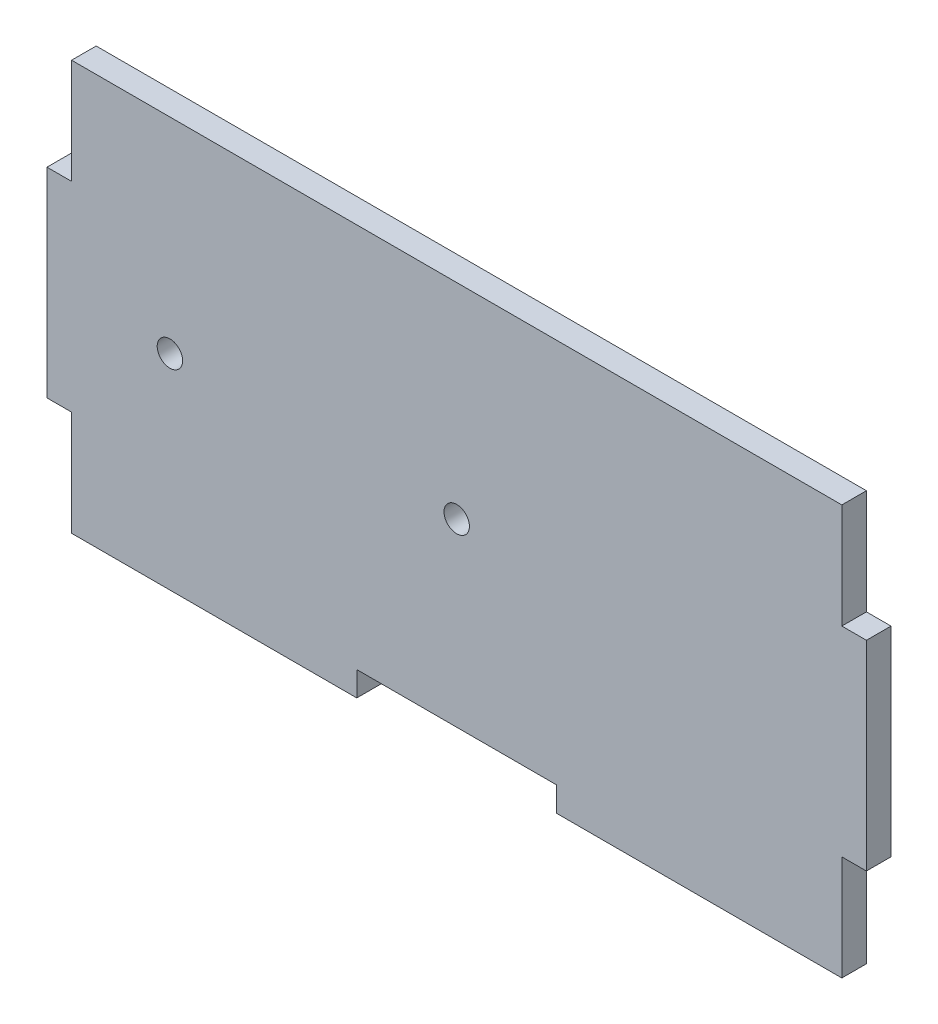
SolidWorks part; units mm, degrees
ref_plane "Alzado" through (0, 0, 0) normal (0, 0, 1) x (1, 0, 0)
ref_plane "Planta" through (0, 0, 0) normal (0, 1, 0) x (1, 0, 0)
ref_plane "Vista lateral" through (0, 0, 0) normal (1, 0, 0) x (0, 0, -1)
sketch "Model" plane through (0, 0, 0) normal (0, 0, 1) x (1, 0, 0)
  line L0 (186, 103) -> (186, 90.195)
  line L1 (186, 90.195) -> (183, 90.195)
  line L2 (183, 90.195) -> (183, 65.805)
  line L3 (183, 65.805) -> (186, 65.805)
  line L4 (186, 65.805) -> (186, 53)
  line L5 (186, 53) -> (220.805, 53)
  line L6 (220.805, 53) -> (220.805, 56)
  line L7 (220.805, 56) -> (245.195, 56)
  line L8 (245.195, 56) -> (245.195, 53)
  line L9 (245.195, 53) -> (269.585, 53)
  line L10 (269.585, 53) -> (280, 53)
  line L11 (280, 53) -> (280, 65.805)
  line L12 (280, 65.805) -> (283, 65.805)
  line L13 (283, 65.805) -> (283, 90.195)
  line L14 (283, 90.195) -> (280, 90.195)
  line L15 (280, 90.195) -> (280, 103)
  line L16 (280, 103) -> (186, 103)
extrude "Saliente-Extruir1" add sketch "Model" along normal blind 3
sketch "Croquis2" plane through (0, 0, 3) normal (0, 0, 1) x (1, 0, 0)
  line L0 (233, 103) -> (233, 56) construction
  line L1 (280, 103) -> (186, 103) construction
  line L2 (220.805, 56) -> (245.195, 56) construction
  line L3 (183, 78) -> (283, 78) construction
  line L4 (183, 90.195) -> (183, 65.805) construction
  line L5 (283, 65.805) -> (283, 90.195) construction
  circle A0 centre (233, 78) radius 1.55
  circle A1 centre (198, 78) radius 1.55
  dimension "D1" = 3.1
  dimension "D2" = 3.1
  dimension "D3" = 35
extrude "Cortar-Extruir1" cut sketch "Croquis2" against normal blind 3
sketch "Croquis3" plane through (0, 0, 3) normal (0, 0, 1) x (1, 0, 0)
  line L0 (233, 76.45) -> (233, 78) construction
  line L1 (233, 78) -> (231.45, 78) construction
  line L2 (198, 76.45) -> (198, 78) construction
  line L3 (198, 78) -> (196.45, 78) construction
  circle A0 centre (233, 78) radius 1.55 construction
  circle A1 centre (198, 78) radius 1.55 construction
